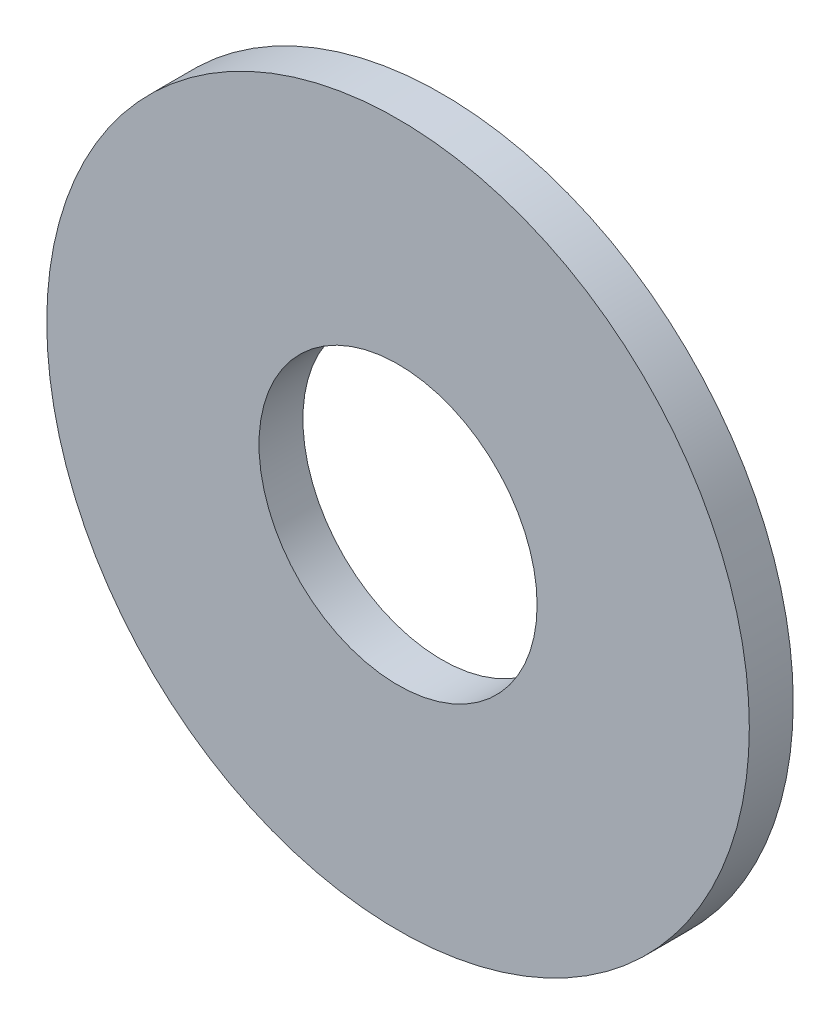
SolidWorks part; units mm, degrees
material "Phosphor bronze 10% D, UNS C52400"
ref_plane "Front" through (0, 0, 0) normal (0, 0, 1) x (1, 0, 0)
ref_plane "Top" through (0, 0, 0) normal (0, 1, 0) x (1, 0, 0)
ref_plane "Right" through (0, 0, 0) normal (1, 0, 0) x (0, 0, -1)
sketch "Sketch1" plane through (0, 0, 0) normal (0, 0, 1) x (1, 0, 0)
  circle A0 centre (0, 0) radius 24
  dimension "D1" = 48
extrude "Boss-Extrude1" add sketch "Sketch1" against normal blind 3
sketch "Sketch2" plane through (0, 0, 0) normal (0, 0, 1) x (1, 0, 0)
  circle A0 centre (0, 0) radius 9.5
  dimension "D1" = 19
extrude "Cut-Extrude1" cut sketch "Sketch2" against normal up to next
